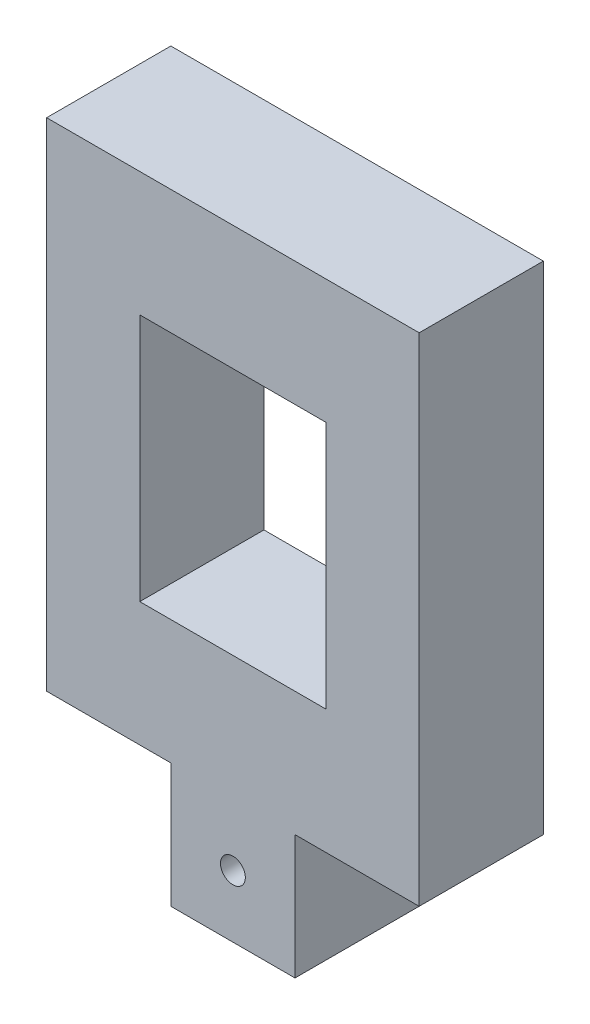
SolidWorks part; units mm, degrees
ref_plane "Front Plane" through (0, 0, 0) normal (0, 0, 1) x (1, 0, 0)
ref_plane "Top Plane" through (0, 0, 0) normal (0, 1, 0) x (1, 0, 0)
ref_plane "Right Plane" through (0, 0, 0) normal (1, 0, 0) x (0, 0, -1)
sketch "Sketch1" plane through (0, 0, 0) normal (0, 0, 1) x (1, 0, 0)
  line L1 (0, 0) -> (19.05, 0)
  line L2 (0, 0) -> (0, 31.75)
  line L3 (0, 31.75) -> (19.05, 31.75)
  line L4 (19.05, 0) -> (19.05, 31.75)
  dimension "D1" = 19.05
  dimension "D2" = 31.75
extrude "Boss-Extrude1" add sketch "Sketch1" along normal blind 6.35
sketch "Sketch2" plane through (0, 0, 6.35) normal (0, 0, 1) x (1, 0, 0)
  line L0 (0, 31.75) -> (0, 0) construction
  line L1 (4.7625, 25.4) -> (14.2875, 25.4)
  line L2 (4.7625, 25.4) -> (4.7625, 12.7)
  line L3 (4.7625, 12.7) -> (14.2875, 12.7)
  line L4 (14.2875, 25.4) -> (14.2875, 12.7)
  line L5 (19.05, 31.75) -> (0, 31.75) construction
  dimension "D1" = 9.525
  dimension "D2" = 12.7
  dimension "D3" = 4.7625
  dimension "D4" = 6.35
extrude "Cut-Extrude1" cut sketch "Sketch2" against normal blind 6.35
sketch "Sketch3" plane through (0, 0, 0) normal (0, 0, -1) x (-1, 0, 0)
  line L0 (-9.525, 0) -> (-9.525, 12.7) construction
  line L1 (-19.05, 0) -> (-12.7, 0)
  line L2 (-19.05, 0) -> (-19.05, 6.35)
  line L3 (-19.05, 6.35) -> (-12.7, 6.35)
  line L4 (-12.7, 0) -> (-12.7, 6.35)
  line L5 (0, 0) -> (-19.05, 0) construction
  line L6 (-4.7625, 12.7) -> (-14.2875, 12.7) construction
  line L7 (-6.35, 0) -> (-6.35, 6.35)
  line L8 (0, 6.35) -> (-6.35, 6.35)
  line L9 (0, 0) -> (0, 6.35)
  line L10 (0, 0) -> (-6.35, 0)
extrude "Cut-Extrude2" cut sketch "Sketch3" against normal through all
sketch "Sketch4" plane through (0, 0, 6.35) normal (0, 0, 1) x (1, 0, 0)
  line L0 (9.525, 3.175) -> (6.35, 3.175) construction
  line L1 (9.525, 3.175) -> (9.525, 6.35) construction
  line L4 (12.7, 6.35) -> (6.35, 6.35)
  line L5 (6.35, 6.35) -> (6.35, 0)
  line L6 (6.35, 0) -> (12.7, 0)
  line L7 (12.7, 0) -> (12.7, 6.35)
  line L8 (12.7, 6.35) -> (6.35, 6.35) construction
  line L9 (6.35, 6.35) -> (6.35, 0) construction
  line L10 (6.35, 0) -> (12.7, 0) construction
  line L11 (12.7, 0) -> (12.7, 6.35) construction
  circle A0 centre (9.525, 3.175) radius 0.635
  dimension "D2" = 1.27
  dimension "D1" = 0
extrude "Cut-Extrude3" cut sketch "Sketch4" against normal through all
